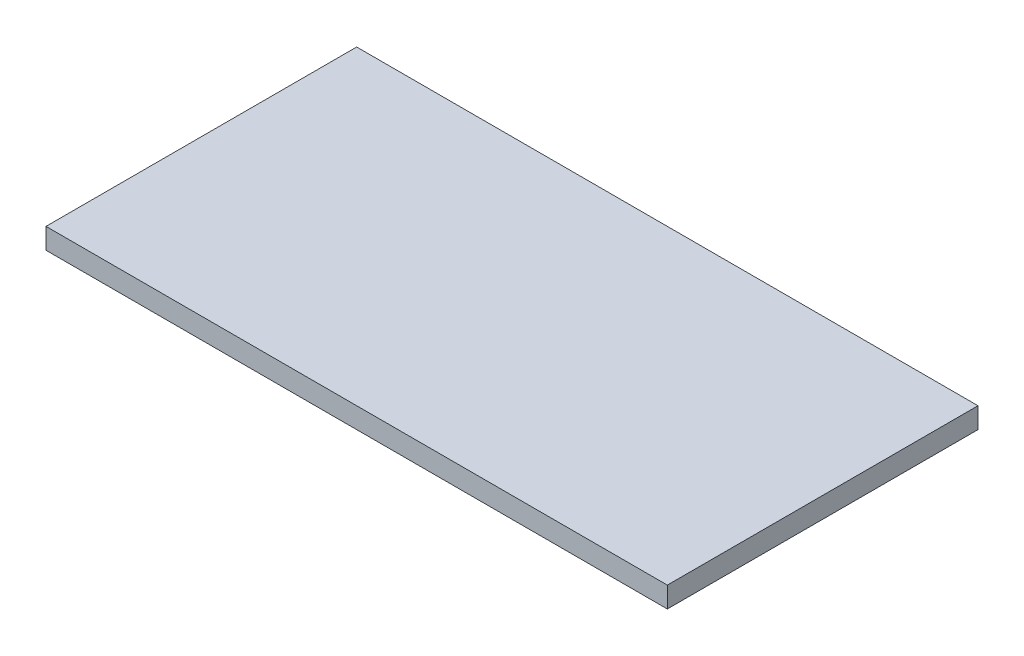
SolidWorks part; units mm, degrees
ref_plane "Front Plane" through (0, 0, 0) normal (0, 0, 1) x (1, 0, 0)
ref_plane "Top Plane" through (0, 0, 0) normal (0, 1, 0) x (1, 0, 0)
ref_plane "Right Plane" through (0, 0, 0) normal (1, 0, 0) x (0, 0, -1)
sketch "Sketch1" plane through (0, 0, 0) normal (0, 1, 0) x (1, 0, 0)
  line L1 (0, 0) -> (300, 0)
  line L2 (0, 0) -> (0, 150)
  line L3 (0, 150) -> (300, 150)
  line L4 (300, 0) -> (300, 150)
extrude "Boss-Extrude1" add sketch "Sketch1" along normal blind 10
